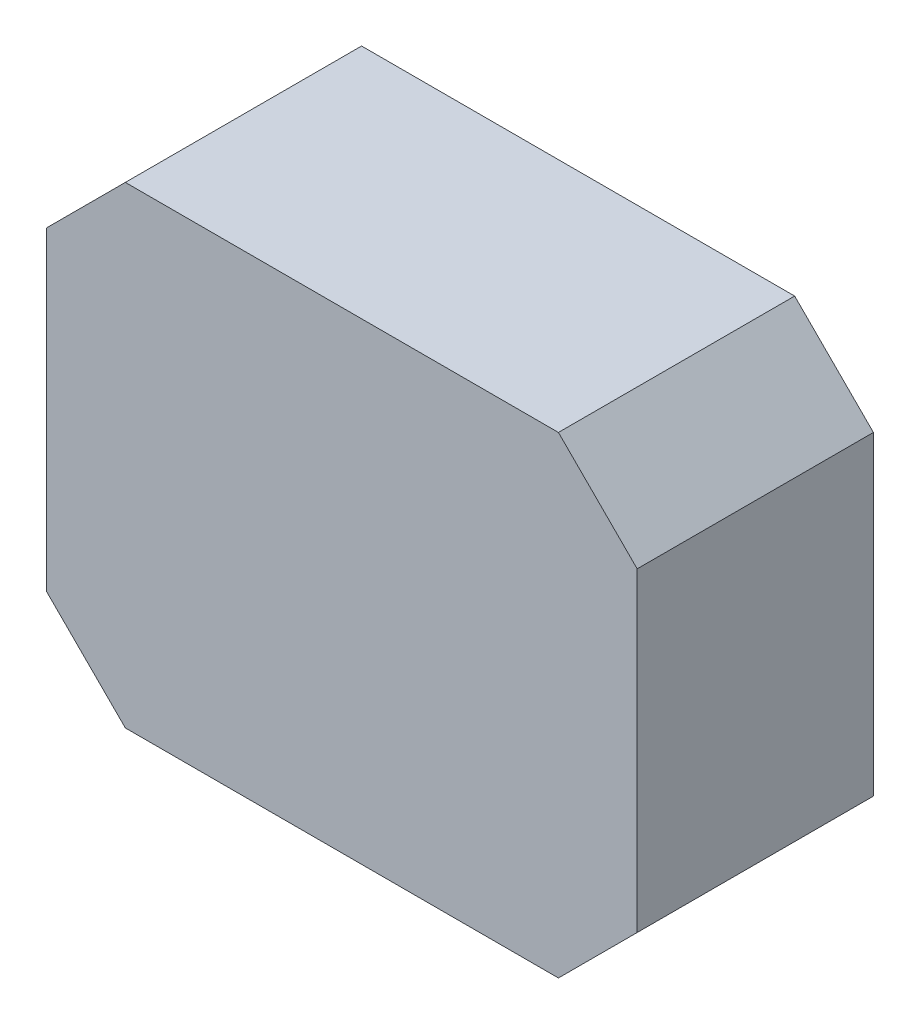
SolidWorks part; units mm, degrees
ref_plane "Front Plane" through (0, 0, 0) normal (0, 0, 1) x (1, 0, 0)
ref_plane "Top Plane" through (0, 0, 0) normal (0, 1, 0) x (1, 0, 0)
ref_plane "Right Plane" through (0, 0, 0) normal (1, 0, 0) x (0, 0, -1)
sketch "Sketch1" plane through (0, 0, 0) normal (0, 0, 1) x (1, 0, 0)
  line L5 (0, 0) -> (150, 0)
  line L6 (0, 0) -> (0, 120)
  line L7 (0, 120) -> (150, 120)
  line L8 (150, 0) -> (150, 120)
  dimension "D1" = 150
  dimension "D2" = 120
extrude "Boss-Extrude1" add sketch "Sketch1" along normal mid plane 60
chamfer "Chamfer1" distance 20 angle 45 4 edges at (150, 0, 0) (0, 0, 0) (150, 120, 0) (0, 120, 0)
